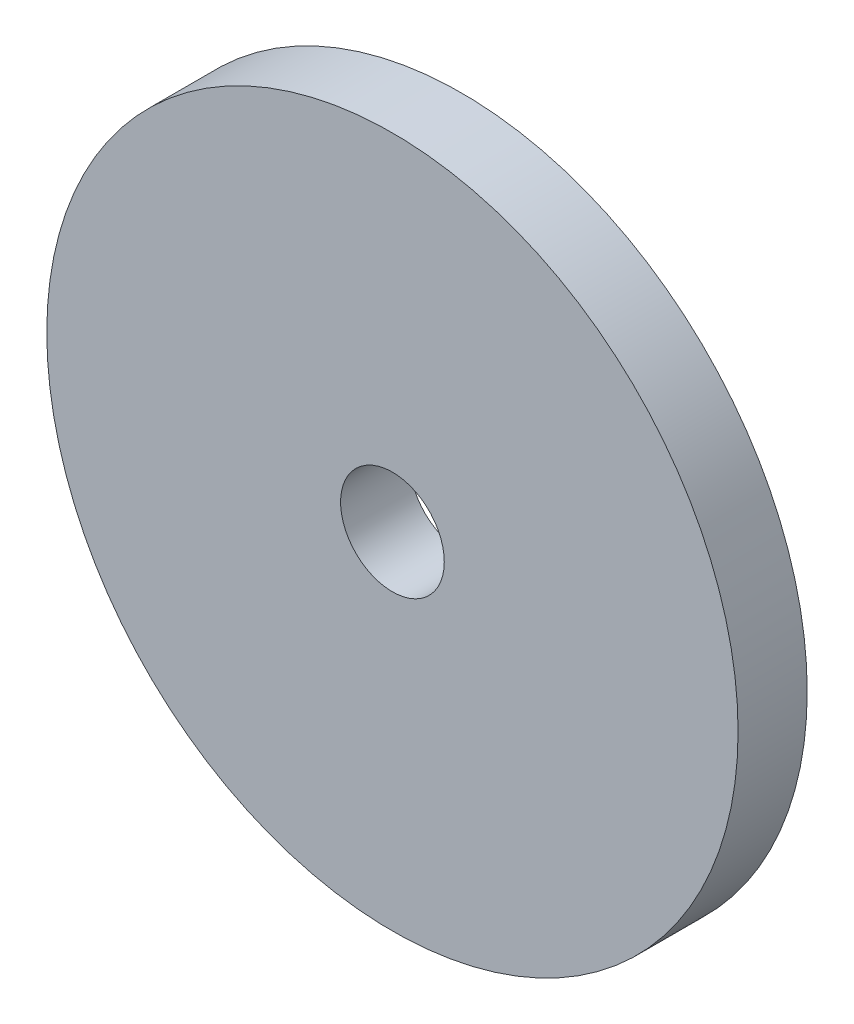
SolidWorks part; units mm, degrees
ref_plane "Front Plane" through (0, 0, 0) normal (0, 0, 1) x (1, 0, 0)
ref_plane "Top Plane" through (0, 0, 0) normal (0, 1, 0) x (1, 0, 0)
ref_plane "Right Plane" through (0, 0, 0) normal (1, 0, 0) x (0, 0, -1)
sketch "Sketch1" plane through (0, 0, 0) normal (0, 0, 1) x (1, 0, 0)
  circle A0 centre (0, 0) radius 1.5
  circle A1 centre (0, 0) radius 10
  dimension "D1" = 3
  dimension "D2" = 20
extrude "Boss-Extrude1" add sketch "Sketch1" along normal blind 2
